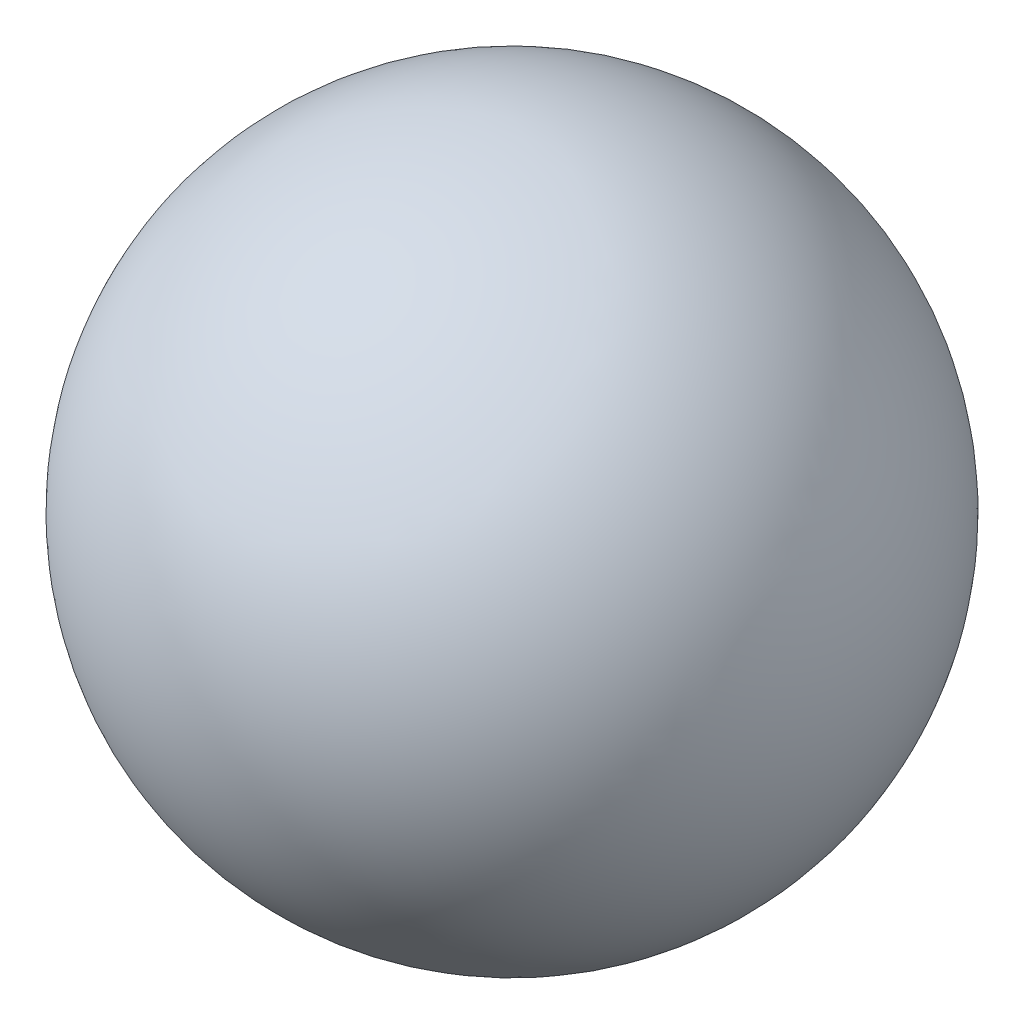
SolidWorks part; units mm, degrees
ref_plane "Front Plane" through (0, 0, 0) normal (0, 0, 1) x (1, 0, 0)
ref_plane "Top Plane" through (0, 0, 0) normal (0, 1, 0) x (1, 0, 0)
ref_plane "Right Plane" through (0, 0, 0) normal (1, 0, 0) x (0, 0, -1)
sketch "Sketch1" plane through (0, 0, 0) normal (0, 1, 0) x (1, 0, 0)
  line L1 (-2.9718, 0) -> (2.9718, 0)
  arc A0 (2.9718, 0) -> (-2.9718, 0) centre (0, 0) ccw
  dimension "D1" = 5.9436
revolve "Revolve1" add sketch "Sketch1" angle 360 about L1
split "Split1"
